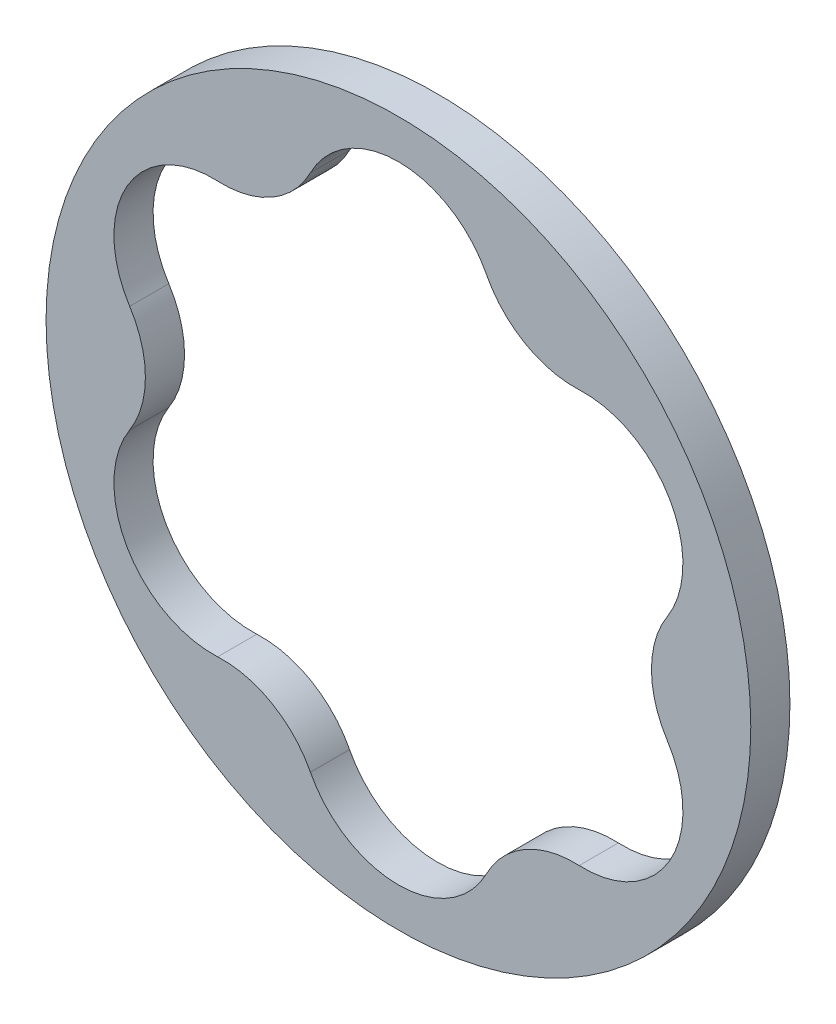
SolidWorks part; units mm, degrees
material "ABS"
ref_plane "Front Plane" through (0, 0, 0) normal (0, 0, 1) x (1, 0, 0)
ref_plane "Top Plane" through (0, 0, 0) normal (0, 1, 0) x (1, 0, 0)
ref_plane "Right Plane" through (0, 0, 0) normal (1, 0, 0) x (0, 0, -1)
sketch "Sketch1" plane through (0, 0, 0) normal (0, 0, 1) x (1, 0, 0)
  circle A0 centre (0, 0) radius 14.2875
  dimension "D1" = 28.575
extrude "Boss-Extrude1" add sketch "Sketch1" along normal mid plane 1.5875
sketch "Sketch2" plane through (0, 0, -0.7937) normal (0, 0, -1) x (-1, 0, 0)
  arc A12 (-7.3297, 8.3524) -> (-3.5686, 10.5239) centre (-7.1372, 12.362) ccw
  arc A13 (-7.3297, 8.3524) -> (-10.8983, 2.1715) centre (-7.5222, 4.3429) ccw
  arc A14 (-10.8983, -2.1715) -> (-10.8983, 2.1715) centre (-14.2744, 0) ccw
  arc A15 (-10.8983, -2.1715) -> (-7.3297, -8.3524) centre (-7.5222, -4.3429) ccw
  arc A16 (-3.5686, -10.5239) -> (-7.3297, -8.3524) centre (-7.1372, -12.362) ccw
  arc A17 (-3.5686, -10.5239) -> (3.5686, -10.5239) centre (0, -8.6859) ccw
  arc A18 (7.3297, -8.3524) -> (3.5686, -10.5239) centre (7.1372, -12.362) ccw
  arc A19 (7.3297, -8.3524) -> (10.8983, -2.1715) centre (7.5222, -4.3429) ccw
  arc A20 (10.8983, 2.1715) -> (10.8983, -2.1715) centre (14.2744, 0) ccw
  arc A21 (10.8983, 2.1715) -> (7.3297, 8.3524) centre (7.5222, 4.3429) ccw
  arc A22 (3.5686, 10.5239) -> (7.3297, 8.3524) centre (7.1372, 12.362) ccw
  arc A23 (3.5686, 10.5239) -> (-3.5686, 10.5239) centre (0, 8.6859) ccw
  arc A24 (-7.3297, 8.3524) -> (-3.5686, 10.5239) centre (-7.1372, 12.362) ccw
  arc A25 (-7.3297, 8.3524) -> (-10.8983, 2.1715) centre (-7.5222, 4.3429) ccw
  arc A26 (-10.8983, -2.1715) -> (-10.8983, 2.1715) centre (-14.2744, 0) ccw
  arc A27 (-10.8983, -2.1715) -> (-7.3297, -8.3524) centre (-7.5222, -4.3429) ccw
  arc A28 (-3.5686, -10.5239) -> (-7.3297, -8.3524) centre (-7.1372, -12.362) ccw
  arc A29 (-3.5686, -10.5239) -> (3.5686, -10.5239) centre (0, -8.6859) ccw
  arc A30 (7.3297, -8.3524) -> (3.5686, -10.5239) centre (7.1372, -12.362) ccw
  arc A31 (7.3297, -8.3524) -> (10.8983, -2.1715) centre (7.5222, -4.3429) ccw
  arc A32 (10.8983, 2.1715) -> (10.8983, -2.1715) centre (14.2744, 0) ccw
  arc A33 (10.8983, 2.1715) -> (7.3297, 8.3524) centre (7.5222, 4.3429) ccw
  arc A34 (3.5686, 10.5239) -> (7.3297, 8.3524) centre (7.1372, 12.362) ccw
  arc A35 (3.5686, 10.5239) -> (-3.5686, 10.5239) centre (0, 8.6859) ccw
  dimension "D1" = 0
extrude "Cut-Extrude1" cut sketch "Sketch2" against normal through all
